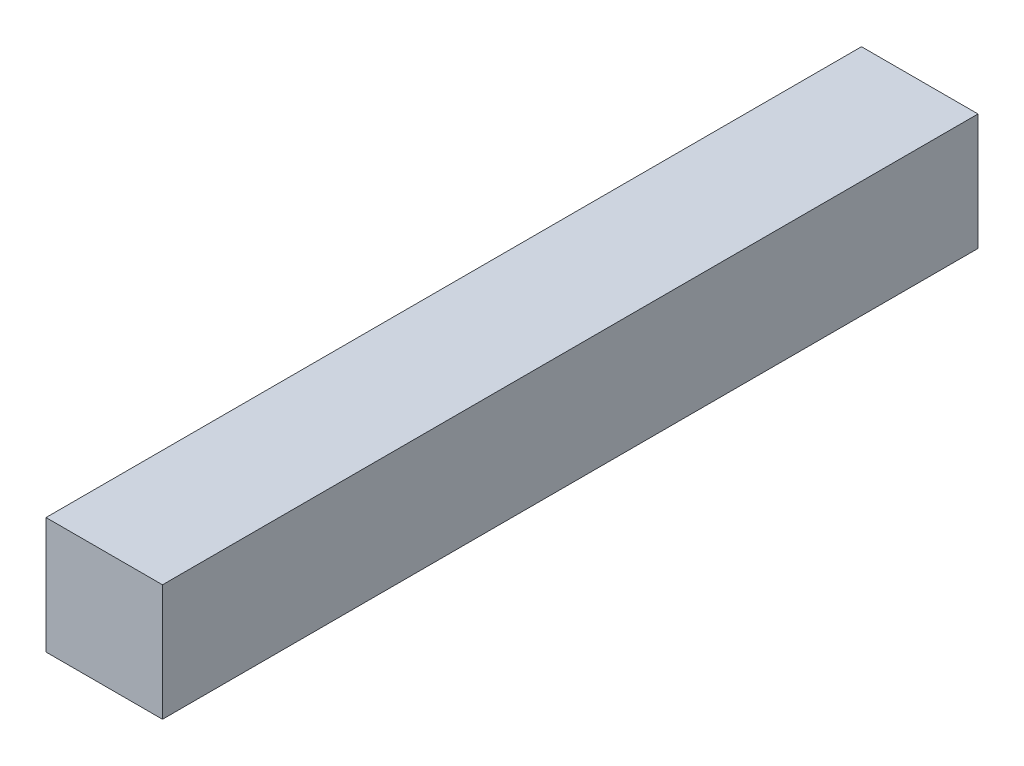
SolidWorks part; units mm, degrees
ref_plane "Front Plane" through (0, 0, 0) normal (0, 0, 1) x (1, 0, 0)
ref_plane "Top Plane" through (0, 0, 0) normal (0, 1, 0) x (1, 0, 0)
ref_plane "Right Plane" through (0, 0, 0) normal (1, 0, 0) x (0, 0, -1)
sketch "Sketch1" plane through (0, 0, 0) normal (0, 0, 1) x (1, 0, 0)
  line L1 (0, 0) -> (25.4, 0)
  line L2 (0, 0) -> (0, 25.4)
  line L3 (0, 25.4) -> (25.4, 25.4)
  line L4 (25.4, 0) -> (25.4, 25.4)
  dimension "D1" = 25.4
  dimension "D2" = 25.4
extrude "Boss-Extrude1" add sketch "Sketch1" along normal blind 177.8
